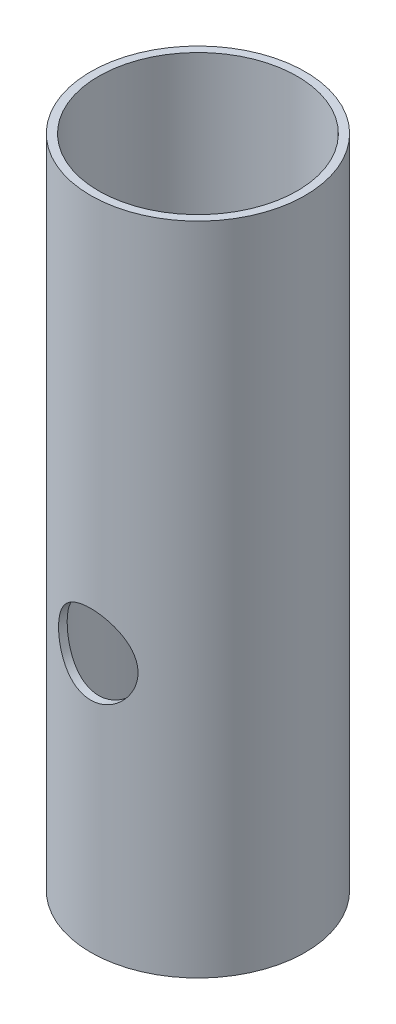
SolidWorks part; units mm, degrees
material "PVC Rigid"
ref_plane "Front Plane" through (0, 0, 0) normal (0, 0, 1) x (1, 0, 0)
ref_plane "Top Plane" through (0, 0, 0) normal (0, 1, 0) x (1, 0, 0)
ref_plane "Right Plane" through (0, 0, 0) normal (1, 0, 0) x (0, 0, -1)
sketch "Sketch1" plane through (0, 0, 0) normal (0, 1, 0) x (1, 0, 0)
  circle A0 centre (0, 0) radius 27
  dimension "D1" = 54
extrude "Boss-Extrude1" add sketch "Sketch1" along normal blind 5
sketch "Sketch2" plane through (0, 5, 0) normal (0, 1, 0) x (1, 0, 0)
  circle A0 centre (0, 0) radius 25
  circle A2 centre (0, 0) radius 27
  dimension "D1" = 50
  dimension "D2" = 54
extrude "Boss-Extrude2" add sketch "Sketch2" along normal blind 160
sketch "Sketch3" plane through (0, 0, 0) normal (0, 0, 1) x (1, 0, 0)
  line L0 (-27, 0) -> (27, 0) construction
  line L1 (27, 0) -> (27, 165) construction
  circle A1 centre (0, 20) radius 5
  dimension "D1" = 10
  dimension "D2" = 20
  dimension "D3" = 27
extrude "Cut-Extrude1" cut sketch "Sketch3" against normal blind 160
sketch "Sketch4" plane through (0, 0, 0) normal (0, 0, 1) x (1, 0, 0)
  line L0 (25, 165) -> (-25, 165) construction
  line L1 (27, 0) -> (27, 165) construction
  circle A0 centre (0, 65) radius 10
  dimension "D1" = 20
  dimension "D2" = 100
  dimension "D3" = 27
extrude "Cut-Extrude6" cut sketch "Sketch4" along normal blind 41 contours A0
